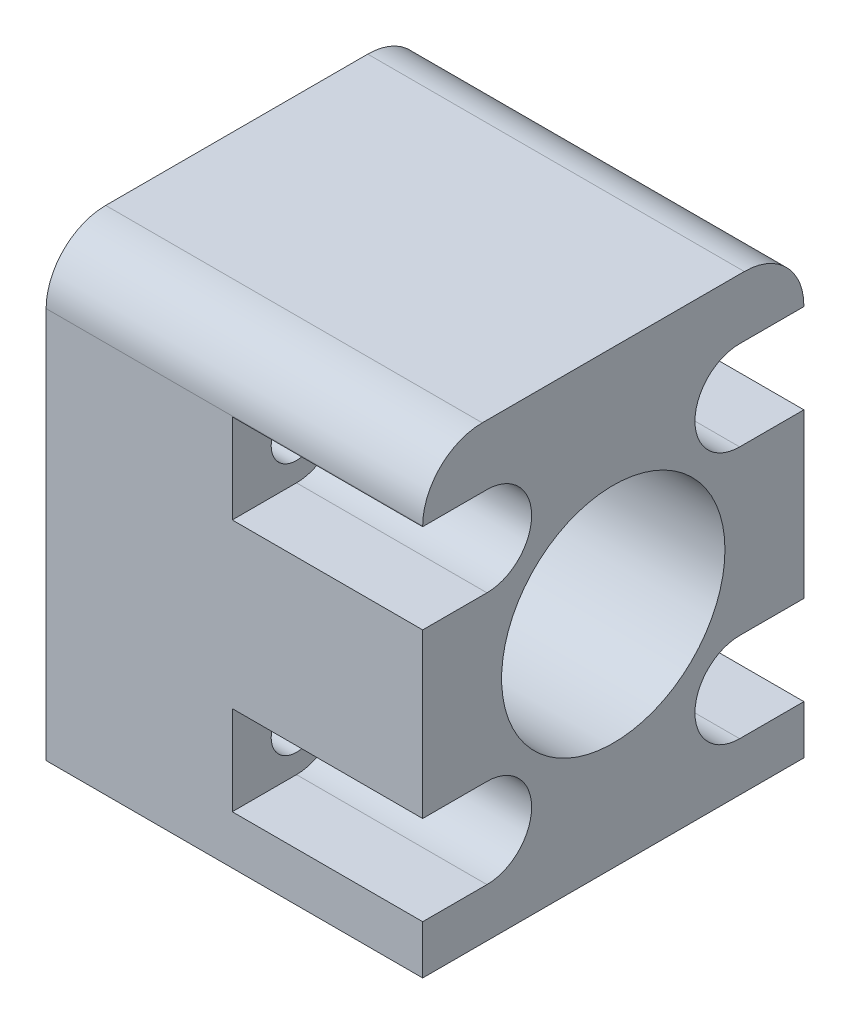
SolidWorks part; units mm, degrees
ref_plane "Plan de face" through (0, 0, 0) normal (0, 0, 1) x (1, 0, 0)
ref_plane "Plan de dessus" through (0, 0, 0) normal (0, 1, 0) x (1, 0, 0)
ref_plane "Plan de droite" through (0, 0, 0) normal (1, 0, 0) x (0, 0, -1)
sketch "Esquisse1" plane through (0, 0, 0) normal (0, 0, 1) x (1, 0, 0)
  line L0 (67.167, -107.583) -> (67.167, -12.4967) construction
  line L1 (67.167, -107.583) -> (118.268, -107.583) construction
  line L2 (67.167, -32.343) -> (118.6716, -32.343) construction
  line L3 (115.367, -14.0613) -> (67.167, -14.0613) construction
  line L4 (115.367, -108.723) -> (115.367, -10.1664) construction
  line L5 (108.4034, -26.123) -> (126.0173, -26.123) construction
  line L6 (91.267, -14.0613) -> (91.267, -17.6404) construction
  line L13 (56.607, -56.8666) -> (109.867, -56.8666) construction
  line L19 (91.267, 2.1061) -> (91.267, -137.8939) construction
  line L20 (61.767, 2.1061) -> (120.767, 2.1061)
  line L21 (61.767, 2.1061) -> (61.767, -137.8939)
  line L22 (61.767, -137.8939) -> (120.767, -137.8939)
  line L23 (120.767, 2.1061) -> (120.767, -137.8939)
  line L24 (61.767, -67.8939) -> (120.767, -67.8939) construction
  circle A0 centre (115.367, -108.723) radius 4
  circle A2 centre (115.367, -26.123) radius 4
  circle A3 centre (74.867, -56.8666) radius 4
  circle A6 centre (67.167, -107.583) radius 4
  circle A7 centre (67.167, -32.343) radius 4
  dimension "D14" = 140
  dimension "D2" = 75.24
  dimension "D3" = 48.2
  dimension "D4" = 6.22
  dimension "D5" = 0
  dimension "D6" = 1.14
  dimension "D15" = 59
extrude "Boss.-Extru.1" add sketch "Esquisse1" along normal blind 25.6
sketch "Esquisse2" plane through (120.767, 0, 0) normal (1, 0, 0) x (0, 0, -1)
  line L0 (-12.8, -125.0284) -> (-21.2853, -133.5136) construction
  line L1 (-12.8, -125.0284) -> (-12.8, -134.7242) construction
  line L2 (-12.8, -95.0284) -> (-21.2853, -103.6294) construction
  line L3 (-12.8, -137.8939) -> (-12.8, 2.1061) construction
  line L4 (-25.6, -137.8939) -> (0, -137.8939) construction
  line L5 (-25.6, 2.1061) -> (0, 2.1061) construction
  line L6 (-12.8, -95.0284) -> (-22.9445, -95.0284) construction
  line L7 (-21.2853, -86.4273) -> (-4.3147, -86.4273) construction
  line L8 (-21.2853, -69.2253) -> (-4.3147, -69.2253) construction
  line L9 (-21.2853, -52.0232) -> (-4.3147, -52.0232) construction
  line L10 (-12.8, -13.4222) -> (-21.2853, -4.9369) construction
  line L11 (-12.8, -125.0284) -> (-17.4685, -125.0284) construction
  line L12 (-12.8, -13.4222) -> (-17.4685, -13.4222) construction
  circle A0 centre (-12.8, -95.0284) radius 7.5
  circle A1 centre (-21.2853, -103.6294) radius 2.6
  circle A2 centre (-4.3147, -103.6294) radius 2.6
  circle A3 centre (-4.3147, -86.4273) radius 2.6
  circle A4 centre (-21.2853, -86.4273) radius 2.6
  circle A5 centre (-21.2853, -133.5136) radius 2.6
  circle A6 centre (-12.8, -125.0284) radius 7.5
  circle A7 centre (-4.3147, -133.5136) radius 2.6
  circle A8 centre (-4.3147, -69.2253) radius 2.6
  circle A9 centre (-21.2853, -69.2253) radius 2.6
  circle A10 centre (-12.8, -77.8263) radius 7.5
  circle A11 centre (-4.3147, -52.0232) radius 2.6
  circle A12 centre (-21.2853, -52.0232) radius 2.6
  circle A13 centre (-12.8, -60.6243) radius 7.5
  circle A14 centre (-4.3147, -34.8212) radius 2.6
  circle A15 centre (-21.2853, -34.8212) radius 2.6
  circle A16 centre (-12.8, -43.4222) radius 7.5
  circle A17 centre (-12.8, -13.4222) radius 7.5
  circle A18 centre (-21.2853, -4.9369) radius 2.6
  circle A19 centre (-4.3147, -4.9369) radius 2.6
  circle A20 centre (-4.3147, -116.5431) radius 2.6
  circle A21 centre (-21.2853, -116.5431) radius 2.6
  circle A22 centre (-4.3147, -21.9075) radius 2.6
  circle A23 centre (-21.2853, -21.9075) radius 2.6
  dimension "D1" = 30
  dimension "D2" = 30
extrude "Enlèv. mat.-Extru.1" cut sketch "Esquisse2" against normal blind 5
sketch "Esquisse3" plane through (120.767, 0, 0) normal (1, 0, 0) x (0, 0, -1)
  circle A0 centre (-12.8, -125.0284) radius 7.5
  circle A1 centre (-12.8, -95.0284) radius 7.5
  circle A2 centre (-12.8, -77.8263) radius 7.5
  circle A3 centre (-12.8, -60.6243) radius 7.5
  circle A4 centre (-12.8, -43.4222) radius 7.5
  circle A5 centre (-12.8, -13.4222) radius 7.5
extrude "Enlèv. mat.-Extru.2" cut sketch "Esquisse3" against normal blind 82
sketch "Esquisse4" plane through (61.767, 0, 0) normal (-1, 0, 0) x (0, 0, 1)
  line L0 (12.8, -13.4222) -> (21.2853, -4.9369) construction
  line L1 (12.8, -13.4222) -> (12.8, -125.0284) construction
  line L2 (12.8, -43.4222) -> (21.2853, -34.9369) construction
  line L3 (12.8, -43.4222) -> (23.3901, -43.4222) construction
  line L4 (12.8, -60.6243) -> (22.7072, -60.6243) construction
  line L5 (12.8, -77.8263) -> (22.0424, -77.8263) construction
  line L6 (12.8, -95.0284) -> (24.6, -95.0284) construction
  line L7 (12.8, -125.0284) -> (4.3147, -133.5136) construction
  line L8 (12.8, -13.4222) -> (17.9951, -13.4222) construction
  line L9 (12.8, -125.0284) -> (17.0426, -125.0284) construction
  circle A0 centre (21.2853, -4.9369) radius 2.6
  circle A1 centre (4.3147, -4.9369) radius 2.6
  circle A2 centre (21.2853, -34.9369) radius 2.6
  circle A3 centre (4.3147, -34.9369) radius 2.6
  circle A4 centre (4.3147, -51.9075) radius 2.6
  circle A5 centre (21.2853, -51.9075) radius 2.6
  circle A6 centre (4.3147, -69.341) radius 2.6
  circle A7 centre (21.2853, -69.341) radius 2.6
  circle A8 centre (4.3147, -86.3116) radius 2.6
  circle A9 centre (21.2853, -86.3116) radius 2.6
  circle A10 centre (4.3147, -103.7451) radius 2.6
  circle A11 centre (21.2853, -103.7451) radius 2.6
  circle A12 centre (4.3147, -133.5136) radius 2.6
  circle A13 centre (21.2853, -133.5136) radius 2.6
  circle A14 centre (4.3147, -21.9075) radius 2.6
  circle A15 centre (21.2853, -21.9075) radius 2.6
  circle A16 centre (4.3147, -116.5431) radius 2.6
  circle A17 centre (21.2853, -116.5431) radius 2.6
extrude "Enlèv. mat.-Extru.3" cut sketch "Esquisse4" against normal blind 5
fillet "Congé1" radius 4 4 edges at (91.267, 2.1061, 25.6) (91.267, 2.1061, 0) (91.267, -137.8939, 0) (91.267, -137.8939, 25.6)
sketch "Esquisse5" plane through (61.767, 0, 0) normal (-1, 0, 0) x (0, 0, 1)
  circle A0 centre (21.2853, -4.9369) radius 1.7
  circle A1 centre (21.2853, -21.9075) radius 1.7
  circle A2 centre (21.2853, -34.9369) radius 1.7
  circle A3 centre (21.2853, -51.9075) radius 1.7
  circle A4 centre (21.2853, -69.341) radius 1.7
  circle A5 centre (21.2853, -86.3116) radius 1.7
  circle A6 centre (21.2853, -103.7451) radius 1.7
  circle A7 centre (21.2853, -116.5431) radius 1.7
  circle A8 centre (21.2853, -133.5136) radius 1.7
  circle A9 centre (4.3147, -4.9369) radius 1.7
  circle A10 centre (4.3147, -21.9075) radius 1.7
  circle A11 centre (4.3147, -34.9369) radius 1.7
  circle A12 centre (4.3147, -51.9075) radius 1.7
  circle A13 centre (4.3147, -69.341) radius 1.7
  circle A14 centre (4.3147, -86.3116) radius 1.7
  circle A15 centre (4.3147, -103.7451) radius 1.7
  circle A16 centre (4.3147, -116.5431) radius 1.7
  circle A17 centre (4.3147, -133.5136) radius 1.7
extrude "Enlèv. mat.-Extru.4" cut sketch "Esquisse5" against normal blind 71
ref_plane "Plan1" through (91.267, 0, 0) normal (-1, 0, 0) x (0, 0, 1)
sketch "Esquisse6" plane through (91.267, 0, 0) normal (-1, 0, 0) x (0, 0, 1)
  line L0 (21.2853, -4.9369) -> (29.2853, -4.9369) construction
  line L1 (21.2853, -1.9369) -> (29.2853, -1.9369)
  line L2 (21.2853, -7.9369) -> (29.2853, -7.9369)
  arc A0 (21.2853, -1.9369) -> (21.2853, -7.9369) centre (21.2853, -4.9369) ccw
  arc A1 (29.2853, -7.9369) -> (29.2853, -1.9369) centre (29.2853, -4.9369) ccw
  point P3 (25.2853, -4.9369)
  line B0 (21.2853, -18.9075) -> (29.2853, -18.9075)
  arc B1 (29.2853, -24.9075) -> (29.2853, -18.9075) centre (29.2853, -21.9075) ccw
  line B2 (21.2853, -24.9075) -> (29.2853, -24.9075)
  arc B3 (21.2853, -18.9075) -> (21.2853, -24.9075) centre (21.2853, -21.9075) ccw
  line B4 (21.2853, -31.9369) -> (29.2853, -31.9369)
  arc B5 (29.2853, -37.9369) -> (29.2853, -31.9369) centre (29.2853, -34.9369) ccw
  line B6 (21.2853, -37.9369) -> (29.2853, -37.9369)
  arc B7 (21.2853, -31.9369) -> (21.2853, -37.9369) centre (21.2853, -34.9369) ccw
  line B8 (21.2853, -48.9075) -> (29.2853, -48.9075)
  arc B9 (29.2853, -54.9075) -> (29.2853, -48.9075) centre (29.2853, -51.9075) ccw
  line B10 (21.2853, -54.9075) -> (29.2853, -54.9075)
  arc B11 (21.2853, -48.9075) -> (21.2853, -54.9075) centre (21.2853, -51.9075) ccw
  line B12 (21.2853, -66.341) -> (29.2853, -66.341)
  arc B13 (29.2853, -72.341) -> (29.2853, -66.341) centre (29.2853, -69.341) ccw
  line B14 (21.2853, -72.341) -> (29.2853, -72.341)
  arc B15 (21.2853, -66.341) -> (21.2853, -72.341) centre (21.2853, -69.341) ccw
  line B16 (21.2853, -83.3116) -> (29.2853, -83.3116)
  arc B17 (29.2853, -89.3116) -> (29.2853, -83.3116) centre (29.2853, -86.3116) ccw
  line B18 (21.2853, -89.3116) -> (29.2853, -89.3116)
  arc B19 (21.2853, -83.3116) -> (21.2853, -89.3116) centre (21.2853, -86.3116) ccw
  line B20 (21.2853, -100.7451) -> (29.2853, -100.7451)
  arc B21 (29.2853, -106.7451) -> (29.2853, -100.7451) centre (29.2853, -103.7451) ccw
  line B22 (21.2853, -106.7451) -> (29.2853, -106.7451)
  arc B23 (21.2853, -100.7451) -> (21.2853, -106.7451) centre (21.2853, -103.7451) ccw
  line B24 (21.2853, -113.5431) -> (29.2853, -113.5431)
  arc B25 (29.2853, -119.5431) -> (29.2853, -113.5431) centre (29.2853, -116.5431) ccw
  line B26 (21.2853, -119.5431) -> (29.2853, -119.5431)
  arc B27 (21.2853, -113.5431) -> (21.2853, -119.5431) centre (21.2853, -116.5431) ccw
  line B28 (21.2853, -130.5136) -> (29.2853, -130.5136)
  arc B29 (29.2853, -136.5136) -> (29.2853, -130.5136) centre (29.2853, -133.5136) ccw
  line B30 (21.2853, -136.5136) -> (29.2853, -136.5136)
  arc B31 (21.2853, -130.5136) -> (21.2853, -136.5136) centre (21.2853, -133.5136) ccw
  line B32 (-3.6853, -1.9369) -> (4.3147, -1.9369)
  arc B33 (4.3147, -7.9369) -> (4.3147, -1.9369) centre (4.3147, -4.9369) ccw
  line B34 (-3.6853, -7.9369) -> (4.3147, -7.9369)
  arc B35 (-3.6853, -1.9369) -> (-3.6853, -7.9369) centre (-3.6853, -4.9369) ccw
  line B36 (-3.6853, -18.9075) -> (4.3147, -18.9075)
  arc B37 (4.3147, -24.9075) -> (4.3147, -18.9075) centre (4.3147, -21.9075) ccw
  line B38 (-3.6853, -24.9075) -> (4.3147, -24.9075)
  arc B39 (-3.6853, -18.9075) -> (-3.6853, -24.9075) centre (-3.6853, -21.9075) ccw
  line B40 (-3.6853, -31.9369) -> (4.3147, -31.9369)
  arc B41 (4.3147, -37.9369) -> (4.3147, -31.9369) centre (4.3147, -34.9369) ccw
  line B42 (-3.6853, -37.9369) -> (4.3147, -37.9369)
  arc B43 (-3.6853, -31.9369) -> (-3.6853, -37.9369) centre (-3.6853, -34.9369) ccw
  line B44 (-3.6853, -48.9075) -> (4.3147, -48.9075)
  arc B45 (4.3147, -54.9075) -> (4.3147, -48.9075) centre (4.3147, -51.9075) ccw
  line B46 (-3.6853, -54.9075) -> (4.3147, -54.9075)
  arc B47 (-3.6853, -48.9075) -> (-3.6853, -54.9075) centre (-3.6853, -51.9075) ccw
  line B48 (-3.6853, -66.341) -> (4.3147, -66.341)
  arc B49 (4.3147, -72.341) -> (4.3147, -66.341) centre (4.3147, -69.341) ccw
  line B50 (-3.6853, -72.341) -> (4.3147, -72.341)
  arc B51 (-3.6853, -66.341) -> (-3.6853, -72.341) centre (-3.6853, -69.341) ccw
  line B52 (-3.6853, -83.3116) -> (4.3147, -83.3116)
  arc B53 (4.3147, -89.3116) -> (4.3147, -83.3116) centre (4.3147, -86.3116) ccw
  line B54 (-3.6853, -89.3116) -> (4.3147, -89.3116)
  arc B55 (-3.6853, -83.3116) -> (-3.6853, -89.3116) centre (-3.6853, -86.3116) ccw
  line B56 (-3.6853, -100.7451) -> (4.3147, -100.7451)
  arc B57 (4.3147, -106.7451) -> (4.3147, -100.7451) centre (4.3147, -103.7451) ccw
  line B58 (-3.6853, -106.7451) -> (4.3147, -106.7451)
  arc B59 (-3.6853, -100.7451) -> (-3.6853, -106.7451) centre (-3.6853, -103.7451) ccw
  line B60 (-3.6853, -113.5431) -> (4.3147, -113.5431)
  arc B61 (4.3147, -119.5431) -> (4.3147, -113.5431) centre (4.3147, -116.5431) ccw
  line B62 (-3.6853, -119.5431) -> (4.3147, -119.5431)
  arc B63 (-3.6853, -113.5431) -> (-3.6853, -119.5431) centre (-3.6853, -116.5431) ccw
  line B64 (-3.6853, -130.5136) -> (4.3147, -130.5136)
  arc B65 (4.3147, -136.5136) -> (4.3147, -130.5136) centre (4.3147, -133.5136) ccw
  line B66 (-3.6853, -136.5136) -> (4.3147, -136.5136)
  arc B67 (-3.6853, -130.5136) -> (-3.6853, -136.5136) centre (-3.6853, -133.5136) ccw
sketch_block_instance "Bloc1-1"
sketch_block "Bloc1" parameters "D1"=2.825
sketch_block_instance "Bloc1-2"
sketch_block_instance "Bloc1-3"
sketch_block_instance "Bloc1-4"
sketch_block_instance "Bloc1-5"
sketch_block_instance "Bloc1-6"
sketch_block_instance "Bloc1-7"
sketch_block_instance "Bloc1-8"
sketch_block_instance "Bloc1-9"
sketch_block_instance "Bloc1-10"
sketch_block_instance "Bloc1-11"
sketch_block_instance "Bloc1-12"
sketch_block_instance "Bloc1-13"
sketch_block_instance "Bloc1-14"
sketch_block_instance "Bloc1-15"
sketch_block_instance "Bloc1-16"
sketch_block_instance "Bloc1-17"
extrude "Enlèv. mat.-Extru.5" cut sketch "Esquisse6" against normal blind 17 and the other way blind 17
sketch "Esquisse7" plane through (0, -137.8939, 0) normal (0, -1, 0) x (1, 0, 0)
  line L1 (29.8831, 36.7343) -> (159.642, 36.7343)
  line L2 (29.8831, 36.7343) -> (29.8831, -11.0547)
  line L3 (29.8831, -11.0547) -> (159.642, -11.0547)
  line L4 (159.642, 36.7343) -> (159.642, -11.0547)
  line L5 (29.8831, 36.7343) -> (159.642, -11.0547) construction
  line L6 (29.8831, -11.0547) -> (159.642, 36.7343) construction
  point P0 (94.7626, 12.8398)
extrude "Enlèv. mat.-Extru.6" cut sketch "Esquisse7" against normal blind 109.7117
sketch "Esquisse8" plane through (120.767, 0, 0) normal (1, 0, 0) x (0, 0, -1)
  line L1 (7.1866, -42.7437) -> (-32.7866, -42.7437)
  line L2 (7.1866, -42.7437) -> (7.1866, 15.8993)
  line L3 (7.1866, 15.8993) -> (-32.7866, 15.8993)
  line L4 (-32.7866, -42.7437) -> (-32.7866, 15.8993)
  line L5 (7.1866, -42.7437) -> (-32.7866, 15.8993) construction
  line L6 (7.1866, 15.8993) -> (-32.7866, -42.7437) construction
  point P0 (-12.8, -13.4222)
extrude "Enlèv. mat.-Extru.7" cut sketch "Esquisse8" against normal blind 33.7117
